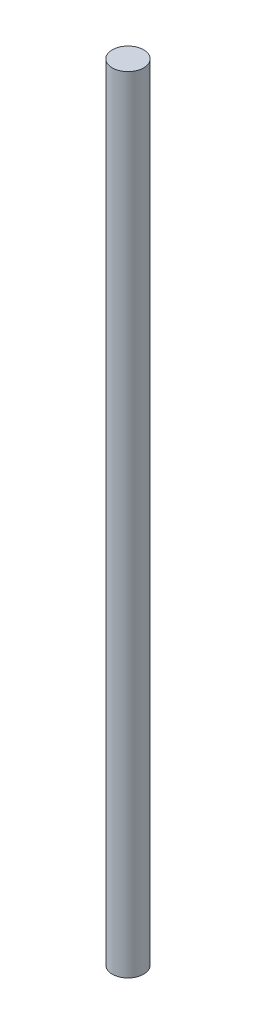
SolidWorks part; units mm, degrees
ref_plane "前视基准面" through (0, 0, 0) normal (0, 0, 1) x (1, 0, 0)
ref_plane "上视基准面" through (0, 0, 0) normal (0, 1, 0) x (1, 0, 0)
ref_plane "右视基准面" through (0, 0, 0) normal (1, 0, 0) x (0, 0, -1)
sketch "草图1" plane through (0, 0, 0) normal (0, 1, 0) x (1, 0, 0)
  circle A0 centre (0, 0) radius 4
  dimension "D1" = 8
extrude "凸台-拉伸1" add sketch "草图1" along normal blind 200
cosmetic thread "装饰螺纹线1" parameters "D2"=7
